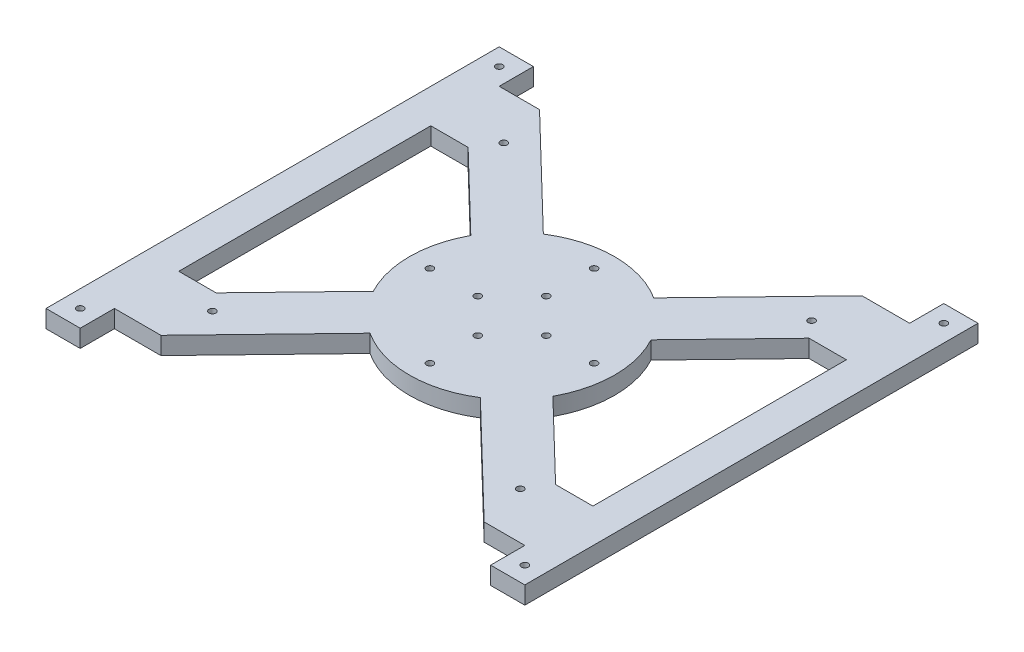
SolidWorks part; units mm, degrees
ref_plane "Front Plane" through (0, 0, 0) normal (0, 0, 1) x (1, 0, 0)
ref_plane "Top Plane" through (0, 0, 0) normal (0, 1, 0) x (1, 0, 0)
ref_plane "Right Plane" through (0, 0, 0) normal (1, 0, 0) x (0, 0, -1)
sketch "Sketch1" plane through (0, 0, 0) normal (0, 1, 0) x (1, 0, 0)
  line L0 (177.8, 168.275) -> (0, 0) construction
  line L1 (12.7, 0) -> (165.1, 0) construction
  line L3 (12.7, 168.275) -> (165.1, 168.275) construction
  line L5 (0, 168.275) -> (177.8, 0) construction
  line L6 (61.728, 168.275) -> (177.8, 45.6329) construction
  line L7 (177.8, 0) -> (165.1, 0)
  line L8 (177.8, 0) -> (177.8, 12.7)
  line L9 (177.8, 12.7) -> (165.1, 12.7) construction
  line L11 (0, 0) -> (12.7, 0)
  line L12 (0, 0) -> (0, 12.7)
  line L13 (0, 12.7) -> (12.7, 12.7) construction
  line L15 (0, 168.275) -> (12.7, 168.275)
  line L18 (12.7, 168.275) -> (12.7, 155.575)
  line L19 (177.8, 168.275) -> (165.1, 168.275)
  line L21 (177.8, 155.575) -> (165.1, 155.575) construction
  line L24 (165.1, 132.0978) -> (165.1, 37.9828)
  line L26 (177.8, 155.575) -> (177.8, 12.7)
  line L28 (165.1, 168.275) -> (165.1, 155.575)
  line L32 (165.1, 12.7) -> (165.1, 0)
  line L33 (165.1, 0) -> (12.7, 0) construction
  line L34 (12.7, 12.7) -> (12.7, 0)
  line L35 (12.7, 155.575) -> (0, 155.575) construction
  line L36 (12.7, 130.175) -> (12.7, 36.5923)
  line L38 (0, 155.575) -> (0, 12.7)
  line L41 (12.7, 130.175) -> (26.5652, 130.175)
  line L45 (12.7, 36.5923) -> (26.5652, 36.5923)
  line L47 (165.1, 12.7) -> (149.9969, 12.7)
  line L49 (165.1, 37.9828) -> (151.2348, 37.9828)
  line L51 (165.1, 155.575) -> (147.4202, 155.575)
  line L53 (165.1, 132.0978) -> (151.2348, 132.0978)
  line L55 (0, 155.575) -> (0, 168.275)
  line L56 (177.8, 155.575) -> (177.8, 168.275)
  line L57 (116.072, 0) -> (0, 122.6421) construction
  line L58 (0, 45.6329) -> (116.072, 168.275) construction
  line L59 (177.8, 122.6421) -> (61.728, 0) construction
  line L60 (147.4202, 155.575) -> (109.4376, 116.2283)
  line L61 (151.2348, 132.0978) -> (122.4203, 102.2483)
  line L62 (151.2348, 37.9828) -> (122.3389, 65.8769)
  line L63 (149.9969, 12.7) -> (109.3168, 51.9697)
  line L64 (26.5652, 36.5923) -> (55.2368, 66.2937)
  line L65 (29.979, 12.7) -> (68.1155, 52.2061)
  line L66 (26.5652, 130.175) -> (55.4193, 102.3213)
  line L67 (27.6818, 155.575) -> (68.4101, 116.2587)
  line L68 (27.6818, 155.575) -> (12.7, 155.575)
  line L69 (29.979, 12.7) -> (12.7, 12.7)
  line L70 (114.4417, 121.4121) -> (128.1476, 108.1814) construction
  line L71 (136.7869, 51.9299) -> (123.5562, 38.224) construction
  line L72 (45.0135, 55.7032) -> (58.7194, 42.4725) construction
  line L73 (48.0459, 135.9169) -> (34.8152, 122.211) construction
  line L74 (177.8, 161.925) -> (0, 161.925) construction
  line L75 (6.35, 168.275) -> (6.35, 0) construction
  line L76 (177.8, 6.35) -> (0, 6.35) construction
  line L77 (171.45, 168.275) -> (171.45, 0) construction
  line L79 (146.05, 138.2259) -> (31.75, 138.2259) construction
  line L80 (146.05, 138.2259) -> (146.05, 30.0491) construction
  line L81 (146.05, 30.0491) -> (31.75, 30.0491) construction
  line L82 (31.75, 138.2259) -> (31.75, 30.0491) construction
  circle A0 centre (88.9, 84.1375) radius 30.48 construction
  circle A1 centre (88.9, 84.1375) radius 12.7 construction
  circle A2 centre (101.6, 84.1375) radius 1.27
  circle A3 centre (88.9, 71.4375) radius 1.27
  circle A4 centre (76.2, 84.1375) radius 1.27
  circle A5 centre (88.9, 96.8375) radius 1.27
  circle A6 centre (119.38, 84.1375) radius 1.27
  circle A7 centre (88.9, 53.6575) radius 1.27
  circle A8 centre (58.42, 84.1375) radius 1.27
  circle A9 centre (88.9, 114.6175) radius 1.27
  arc A10 (109.4376, 116.2283) -> (68.4101, 116.2587) centre (88.9, 84.1375) ccw
  arc A11 (122.3389, 65.8769) -> (122.4203, 102.2483) centre (88.9, 84.1375) ccw
  arc A12 (68.1155, 52.2061) -> (109.3168, 51.9697) centre (88.9, 84.1375) ccw
  arc A13 (55.4193, 102.3213) -> (55.2368, 66.2937) centre (88.9, 84.1375) ccw
  circle A14 centre (171.45, 161.925) radius 1.27
  circle A15 centre (171.45, 6.35) radius 1.27
  circle A16 centre (6.35, 6.35) radius 1.27
  circle A17 centre (6.35, 161.925) radius 1.27
  circle A18 centre (146.05, 138.2259) radius 1.27
  circle A19 centre (146.05, 30.0491) radius 1.27
  circle A20 centre (31.75, 30.0491) radius 1.27
  circle A21 centre (31.75, 138.2259) radius 1.27
  point P55 (121.2946, 114.7967)
  point P68 (130.1715, 45.077)
  point P73 (41.4306, 129.0639)
  point P74 (51.8664, 49.0879)
  dimension "D4" = 60.96
  dimension "D5" = 25.4
  dimension "D6" = 76.2
  dimension "D9" = 2.54
  dimension "D1" = 168.275
  dimension "D2" = 177.8
  dimension "D3" = 12.7
  dimension "D7" = 25.4
  dimension "D8" = 19.05
  dimension "D10" = 12.7
  dimension "D11" = 12.7
  dimension "D12" = 114.3
extrude "Boss-Extrude1" add sketch "Sketch1" along normal blind 6.5278
equation "\"D1@Sketch1\"=6+5/8"
equation "\"width\"= \"D7@Sketch1\""
